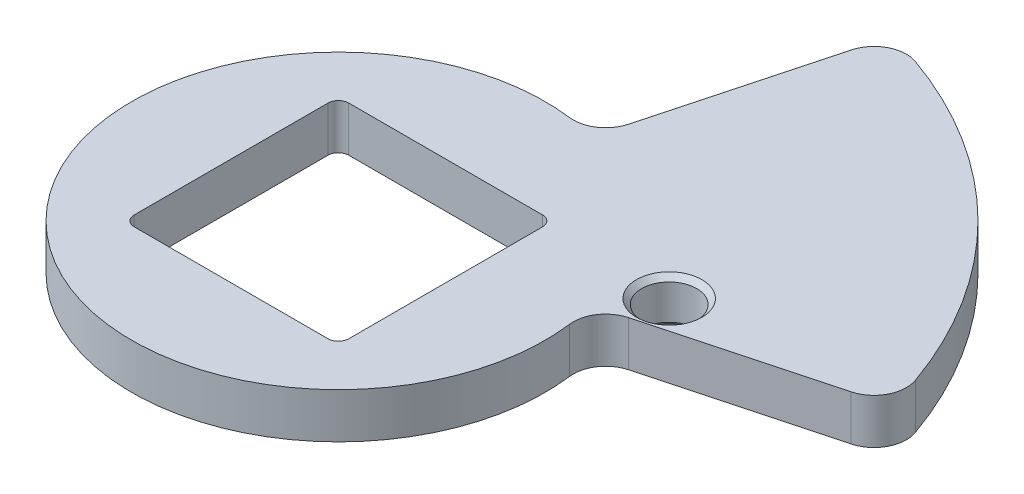
SolidWorks part; units mm, degrees
ref_plane "Front Plane" through (0, 0, 0) normal (0, 0, 1) x (1, 0, 0)
ref_plane "Top Plane" through (0, 0, 0) normal (0, 1, 0) x (1, 0, 0)
ref_plane "Right Plane" through (0, 0, 0) normal (1, 0, 0) x (0, 0, -1)
sketch "Sketch2" plane through (0, 0, 0) normal (0, 1, 0) x (1, 0, 0)
  line L0 (-22.9472, 0) -> (26.77, 0) construction
  line L1 (0, -24.0324) -> (0, 26.4325) construction
  line L2 (0, 0) -> (27.2097, 27.2097) construction
  line L3 (11.5045, 42.9354) -> (5.2592, 19.6276)
  line L4 (42.9354, 11.5045) -> (19.6276, 5.2592)
  line L5 (19.6276, 5.2592) -> (0, 0) construction
  line L7 (-10.541, 10.541) -> (10.541, 10.541)
  line L8 (-10.541, 10.541) -> (-10.541, -10.541)
  line L9 (-10.541, -10.541) -> (10.541, -10.541)
  line L10 (10.541, 10.541) -> (10.541, -10.541)
  line L11 (-10.541, 10.541) -> (10.541, -10.541) construction
  line L12 (-10.541, -10.541) -> (10.541, 10.541) construction
  arc A0 (5.2592, 19.6276) -> (19.6276, 5.2592) centre (0, 0) ccw
  arc A1 (11.5045, 42.9354) -> (42.9354, 11.5045) centre (0, 0) cw
  circle A2 centre (22.86, 9.652) radius 2.7068
  dimension "D1" = 40.64
  dimension "D3" = 15
  dimension "D4" = 44.45
  dimension "D2" = 45
  dimension "D5" = 21.082
  dimension "D6" = 9.652
  dimension "D7" = 22.86
extrude "Boss-Extrude1" add sketch "Sketch2" along normal blind 4.445
fillet "Fillet1" radius 3.175 4 edges at (5.2592, 2.2225, -19.6276) (11.5045, 2.2225, -42.9354) (42.9354, 2.2225, -11.5045) (19.6276, 2.2225, -5.2592)
fillet "Fillet2" radius 1.016 4 edges at (10.541, 2.2225, -10.541) (-10.541, 2.2225, -10.541) (10.541, 2.2225, 10.541) (-10.541, 2.2225, 10.541)
chamfer "Chamfer1" distance 0.508 angle 45 2 edges at (22.86, 0, -6.9452) (22.86, 4.445, -6.9452)
